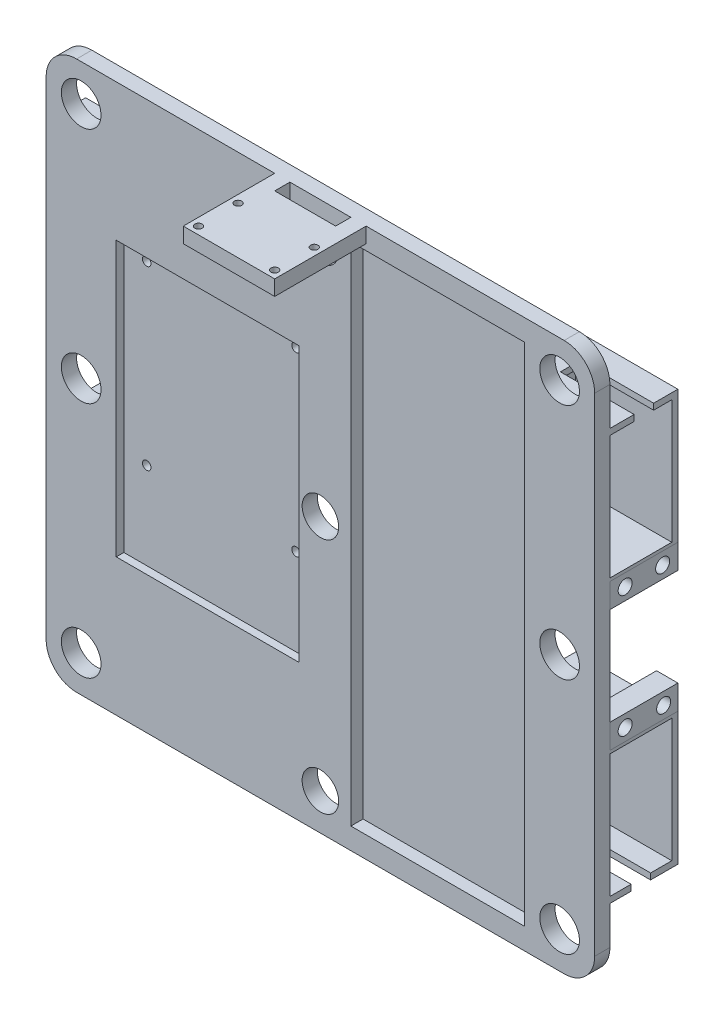
SolidWorks part; units mm, degrees
ref_plane "Front Plane" through (0, 0, 0) normal (0, 0, 1) x (1, 0, 0)
ref_plane "Top Plane" through (0, 0, 0) normal (0, 1, 0) x (1, 0, 0)
ref_plane "Right Plane" through (0, 0, 0) normal (1, 0, 0) x (0, 0, -1)
sketch "Sketch1" plane through (0, 0, 0) normal (0, 0, 1) x (1, 0, 0)
  line L1 (90, 90) -> (-90, 90)
  line L2 (90, 90) -> (90, -90)
  line L3 (90, -90) -> (-90, -90)
  line L4 (-90, 90) -> (-90, -90)
  line L5 (90, 90) -> (-90, -90) construction
  line L6 (90, -90) -> (-90, 90) construction
  point P0 (0, 0)
  dimension "D1" = 180
extrude "Boss-Extrude1" add sketch "Sketch1" along normal blind 5
sketch "Sketch2" plane through (0, 0, 5) normal (0, 0, 1) x (1, 0, 0)
  line L0 (-90, 90) -> (-90, -90) construction
  line L1 (-67, 45) -> (-7, 45)
  line L2 (-67, 45) -> (-67, -45)
  line L3 (-67, -45) -> (-7, -45)
  line L4 (-7, 45) -> (-7, -45)
  point P8 (-7, 0)
  dimension "D1" = 23
  dimension "D2" = 60
  dimension "D3" = 90
extrude "Cut-Extrude1" cut sketch "Sketch2" against normal blind 2.5
sketch "Sketch3" plane through (0, 0, 2.5) normal (0, 0, 1) x (1, 0, 0)
  line L0 (-7, -45) -> (-7, 45) construction
  line L1 (-7, 45) -> (-67, 45) construction
  circle A0 centre (-10.5, 41.5) radius 1.4
  circle A1 centre (-59.5, 41.5) radius 1.4
  circle A2 centre (-59.5, -16.5) radius 1.4
  circle A3 centre (-10.5, -16.5) radius 1.4
  dimension "D1" = 2.8
  dimension "D2" = 3.5
  dimension "D3" = 49
  dimension "D4" = 58
  dimension "D5" = 3.5
extrude "Cut-Extrude2" cut sketch "Sketch3" against normal blind 2.5
sketch "Sketch4" plane through (0, 0, 5) normal (0, 0, 1) x (1, 0, 0)
  line L0 (90, -90) -> (90, 90) construction
  line L1 (10, 83) -> (67, 83)
  line L2 (10, 83) -> (10, -83)
  line L3 (10, -83) -> (67, -83)
  line L4 (67, 83) -> (67, -83)
  point P4 (10, 0)
  dimension "D1" = 57
  dimension "D2" = 166
  dimension "D3" = 23
extrude "Cut-Extrude3" cut sketch "Sketch4" against normal blind 4
sketch "Sketch6" plane through (0, 0, 0) normal (0, 0, -1) x (-1, 0, 0)
  line L0 (90, 90) -> (90, -90) construction
  line L1 (90, 65.5) -> (58.4, 65.5)
  line L3 (90, 25) -> (58.4, 25)
  line L4 (58.4, 65.5) -> (58.4, 25)
  line L5 (-90, -90) -> (-90, 90) construction
  line L6 (90, -25) -> (58.4, -25)
  line L8 (90, -65.5) -> (58.4, -65.5)
  line L9 (58.4, -25) -> (58.4, -65.5)
  line L10 (-90, -25) -> (-58.4, -25)
  line L12 (-90, -65.5) -> (-58.4, -65.5)
  line L13 (-58.4, -25) -> (-58.4, -65.5)
  line L14 (-58.4, 65.5) -> (-58.4, 90) construction
  line L15 (-90, 65.5) -> (-58.4, 65.5)
  line L17 (-90, 25) -> (-58.4, 25)
  line L18 (-58.4, 65.5) -> (-58.4, 25)
  line L19 (-90, 90) -> (90, 90) construction
  line L20 (-58.4, 25) -> (-58.4, -25) construction
  line L21 (-58.4, -65.5) -> (-58.4, -90) construction
  line L22 (90, -90) -> (-90, -90) construction
  line L23 (58.4, 65.5) -> (58.4, 90) construction
  line L24 (58.4, 25) -> (58.4, -25) construction
  line L25 (58.4, -65.5) -> (58.4, -90) construction
  line L26 (-90, 65.5) -> (-90, 67.5)
  line L27 (-90, 67.5) -> (-56.4, 67.5)
  line L28 (-56.4, 67.5) -> (-56.4, 24)
  line L29 (-56.4, 24) -> (-90, 24)
  line L30 (-90, 24) -> (-90, 25)
  line L31 (-90, -25) -> (-90, -24)
  line L32 (-90, -24) -> (-56.4, -24)
  line L33 (-56.4, -24) -> (-56.4, -67.5)
  line L34 (-56.4, -67.5) -> (-90, -67.5)
  line L35 (-90, -67.5) -> (-90, -65.5)
  line L36 (90, 65.5) -> (90, 67.5)
  line L37 (90, 67.5) -> (56.4, 67.5)
  line L38 (56.4, 67.5) -> (56.4, 24)
  line L39 (56.4, 24) -> (90, 24)
  line L40 (90, 24) -> (90, 25)
  line L41 (90, -25) -> (90, -24)
  line L42 (90, -24) -> (56.4, -24)
  line L43 (56.4, -24) -> (56.4, -67.5)
  line L44 (56.4, -67.5) -> (90, -67.5)
  line L45 (90, -67.5) -> (90, -65.5)
  dimension "D1" = 40.5
  dimension "D2" = 40.5
  dimension "D3" = 40.5
  dimension "D4" = 40.5
  dimension "D5" = 31.6
  dimension "D6" = 31.6
  dimension "D7" = 31.6
  dimension "D8" = 31.6
  dimension "D9" = 50
  dimension "D10" = 2
  dimension "D11" = 2
  dimension "D12" = 1
  dimension "D13" = 1
  dimension "D14" = 2
  dimension "D15" = 2
  dimension "D16" = 2
  dimension "D17" = 2
  dimension "D18" = 1
  dimension "D19" = 1
  dimension "D20" = 2
  dimension "D21" = 2
extrude "Boss-Extrude2" add sketch "Sketch6" along normal blind 20.3
sketch "Sketch7" plane through (0, 0, -20.3) normal (0, 0, -1) x (-1, 0, 0)
  line L1 (-90, 67.5) -> (-56.4, 67.5)
  line L2 (-90, 67.5) -> (-90, 24)
  line L3 (-90, 24) -> (-56.4, 24)
  line L4 (-56.4, 67.5) -> (-56.4, 24)
  line L5 (-90, -24) -> (-56.4, -24)
  line L6 (-90, -24) -> (-90, -67.5)
  line L7 (-90, -67.5) -> (-56.4, -67.5)
  line L8 (-56.4, -24) -> (-56.4, -67.5)
  line L9 (56.4, -24) -> (90, -24)
  line L10 (56.4, -24) -> (56.4, -67.5)
  line L11 (56.4, -67.5) -> (90, -67.5)
  line L12 (90, -24) -> (90, -67.5)
  line L13 (56.4, 67.5) -> (90, 67.5)
  line L14 (56.4, 67.5) -> (56.4, 24)
  line L15 (56.4, 24) -> (90, 24)
  line L16 (90, 67.5) -> (90, 24)
extrude "Boss-Extrude3" add sketch "Sketch7" along normal blind 2
sketch "Sketch8" plane through (90, 0, 0) normal (1, 0, 0) x (0, 0, -1)
  line L0 (20.3, -65.5) -> (0, -65.5) construction
  line L1 (6.95, -65.5) -> (13.35, -65.5)
  line L2 (6.95, -65.5) -> (6.95, -67.5)
  line L3 (6.95, -67.5) -> (13.35, -67.5)
  line L4 (13.35, -65.5) -> (13.35, -67.5)
  line L5 (22.3, -67.5) -> (0, -67.5) construction
  line L6 (22.3, 67.5) -> (0, 67.5) construction
  line L7 (7.95, 67.5) -> (14.35, 67.5)
  line L8 (7.95, 67.5) -> (7.95, 65.5)
  line L9 (7.95, 65.5) -> (14.35, 65.5)
  line L10 (14.35, 67.5) -> (14.35, 65.5)
  line L11 (20.3, 65.5) -> (0, 65.5) construction
  point P8 (10.15, -65.5)
  point P9 (10.15, -65.5)
  point P18 (11.15, 67.5)
  point P19 (11.15, 67.5)
  dimension "D1" = 6.4
  dimension "D2" = 6.4
extrude "Cut-Extrude5" cut sketch "Sketch8" against normal blind 24.2
sketch "Sketch9" plane through (90, 0, 0) normal (1, 0, 0) x (0, 0, -1)
  line L1 (0, 24) -> (22.3, 24)
  line L2 (0, 24) -> (0, 16)
  line L3 (0, 16) -> (22.3, 16)
  line L4 (22.3, 24) -> (22.3, 16)
  line L5 (0, -24) -> (22.3, -24)
  line L6 (0, -24) -> (0, -16)
  line L7 (0, -16) -> (22.3, -16)
  line L8 (22.3, -24) -> (22.3, -16)
  line L10 (22.3, -24) -> (22.3, -67.5) construction
  dimension "D1" = 8
extrude "Boss-Extrude4" add sketch "Sketch9" against normal blind 7 separate body
sketch "Sketch12" plane through (-90, 0, 0) normal (-1, 0, 0) x (0, 0, 1)
  line L1 (-22.3, 24) -> (0, 24)
  line L2 (-22.3, 24) -> (-22.3, 16)
  line L3 (-22.3, 16) -> (0, 16)
  line L4 (0, 24) -> (0, 16)
  line L5 (0, -24) -> (-22.3, -24)
  line L6 (0, -24) -> (0, -16)
  line L7 (0, -16) -> (-22.3, -16)
  line L8 (-22.3, -24) -> (-22.3, -16)
extrude "Boss-Extrude5" add sketch "Sketch12" against normal blind 7
sketch "Sketch11" plane through (-90, 0, 0) normal (-1, 0, 0) x (0, 0, 1)
  line L0 (-22.3, 67.5) -> (0, 67.5) construction
  line L1 (-14.35, 67.5) -> (-7.95, 67.5)
  line L2 (-14.35, 67.5) -> (-14.35, 65.5)
  line L3 (-14.35, 65.5) -> (-7.95, 65.5)
  line L4 (-7.95, 67.5) -> (-7.95, 65.5)
  line L5 (-20.3, 65.5) -> (0, 65.5) construction
  line L6 (-20.3, -65.5) -> (0, -65.5) construction
  line L7 (-13.35, -65.5) -> (-6.95, -65.5)
  line L8 (-13.35, -65.5) -> (-13.35, -67.5)
  line L9 (-13.35, -67.5) -> (-6.95, -67.5)
  line L10 (-6.95, -65.5) -> (-6.95, -67.5)
  line L11 (-22.3, -67.5) -> (0, -67.5) construction
  line L12 (-20.3, -65.5) -> (0, -65.5) construction
  point P18 (-10.15, -65.5)
  point P19 (-10.15, -65.5)
  point P20 (-11.15, 67.5)
  point P21 (-11.15, 67.5)
  dimension "D1" = 6.4
  dimension "D2" = 6.4
extrude "Cut-Extrude7" cut sketch "Sketch11" against normal blind 24.2
sketch "Sketch10" plane through (90, 0, 0) normal (1, 0, 0) x (0, 0, -1)
  line L0 (20.3, -25) -> (0, -25) construction
  line L1 (20.3, 25) -> (0, 25) construction
  line L2 (0, 24) -> (0, 16) construction
  line L3 (22.3, 16) -> (22.3, 24) construction
  line L4 (0, -16) -> (0, -24) construction
  line L5 (22.3, -24) -> (22.3, -16) construction
  circle A0 centre (5, 20) radius 2.3
  circle A1 centre (17.3, 20) radius 2.3
  circle A2 centre (5, -20) radius 2.3
  circle A3 centre (17.6353, -20) radius 2.3
  dimension "D1" = 4.6
  dimension "D2" = 5
  dimension "D3" = 5
  dimension "D4" = 5
  dimension "D5" = 5
  dimension "D6" = 5
  dimension "D7" = 4.6647
extrude "Cut-Extrude6" cut sketch "Sketch10" against normal through all
sketch "Sketch13" plane through (0, 0, 5) normal (0, 0, 1) x (1, 0, 0)
  line L0 (90, -90) -> (90, 90) construction
  line L1 (-90, 90) -> (-90, -90) construction
  line L5 (90, 90) -> (-90, 90) construction
  line L6 (-90, -90) -> (90, -90) construction
  line L7 (0, 78) -> (0, 39) construction
  line L8 (0, 39) -> (0, 0) construction
  line L9 (0, 0) -> (0, -39) construction
  line L10 (0, -39) -> (0, -78) construction
  circle A0 centre (78.5, 78) radius 6.5
  circle A1 centre (78.5, 0) radius 6.5
  circle A2 centre (78.5, -78) radius 6.5
  circle A3 centre (-78.5, 78) radius 6.5
  circle A4 centre (-78.5, 0) radius 6.5
  circle A5 centre (-78.5, -78) radius 6.5
  circle A6 centre (0, 0) radius 6
  circle A9 centre (0, 78) radius 6
  circle A10 centre (0, -78) radius 6
  dimension "D1" = 13
  dimension "D6" = 12
  dimension "D2" = 11.5
  dimension "D3" = 11.5
  dimension "D4" = 12
  dimension "D5" = 12
extrude "Cut-Extrude8" cut sketch "Sketch13" against normal through all
fillet "Fillet1" radius 10 4 edges at (-90, -90, 2.5) (90, -90, 2.5) (90, 90, 2.5) (-90, 90, 2.5)
sketch "Sketch14" plane through (0, 90, 0) normal (0, 1, 0) x (1, 0, 0)
  line L0 (-15, 0) -> (-15, -35)
  line L1 (80, 0) -> (-80, 0) construction
  line L2 (-15, -35) -> (15, -35)
  line L3 (15, -35) -> (15, 0)
  line L4 (15, 0) -> (10, 0)
  line L5 (10, 0) -> (10, -10)
  line L6 (10, -10) -> (-10, -10)
  line L7 (-10, -10) -> (-10, 0)
  line L8 (-10, 0) -> (-15, 0)
  line L9 (80, -5) -> (-80, -5) construction
  point P6 (0, -10)
  dimension "D1" = 5
  dimension "D2" = 25
  dimension "D3" = 5
  dimension "D4" = 20
extrude "Boss-Extrude6" add sketch "Sketch14" against normal blind 5
sketch "Sketch15" plane through (0, 90, 0) normal (0, 1, 0) x (1, 0, 0)
  line L0 (-15, -5) -> (-15, -35) construction
  line L1 (15, -35) -> (15, -5) construction
  line L2 (-15, -35) -> (15, -35) construction
  circle A0 centre (-12.5, -32.5) radius 1.2
  circle A1 centre (12.5, -32.5) radius 1.2
  circle A2 centre (-12.5, -19.5) radius 1.2
  circle A3 centre (12.5, -19.5) radius 1.2
  dimension "D3" = 2.4
  dimension "D1" = 2.5
  dimension "D2" = 2.5
  dimension "D4" = 2.5
  dimension "D5" = 13
extrude "Cut-Extrude9" cut sketch "Sketch15" against normal through all
